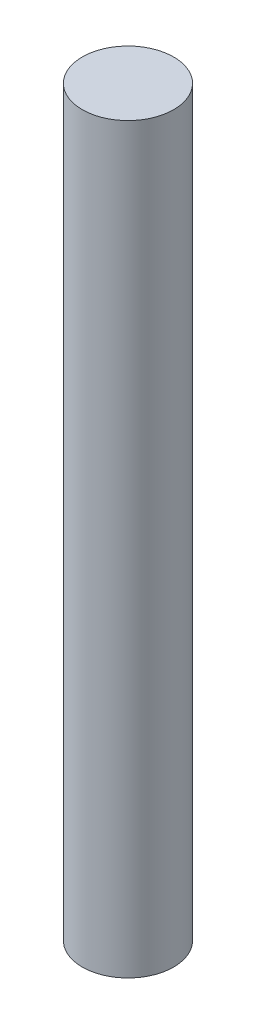
SolidWorks part; units mm, degrees
ref_plane "Front Plane" through (0, 0, 0) normal (0, 0, 1) x (1, 0, 0)
ref_plane "Top Plane" through (0, 0, 0) normal (0, 1, 0) x (1, 0, 0)
ref_plane "Right Plane" through (0, 0, 0) normal (1, 0, 0) x (0, 0, -1)
sketch "Sketch1" plane through (0, 0, 0) normal (0, 1, 0) x (1, 0, 0)
  circle A0 centre (0, 0) radius 4
  dimension "D1" = 8
extrude "Boss-Extrude1" add sketch "Sketch1" along normal blind 65
